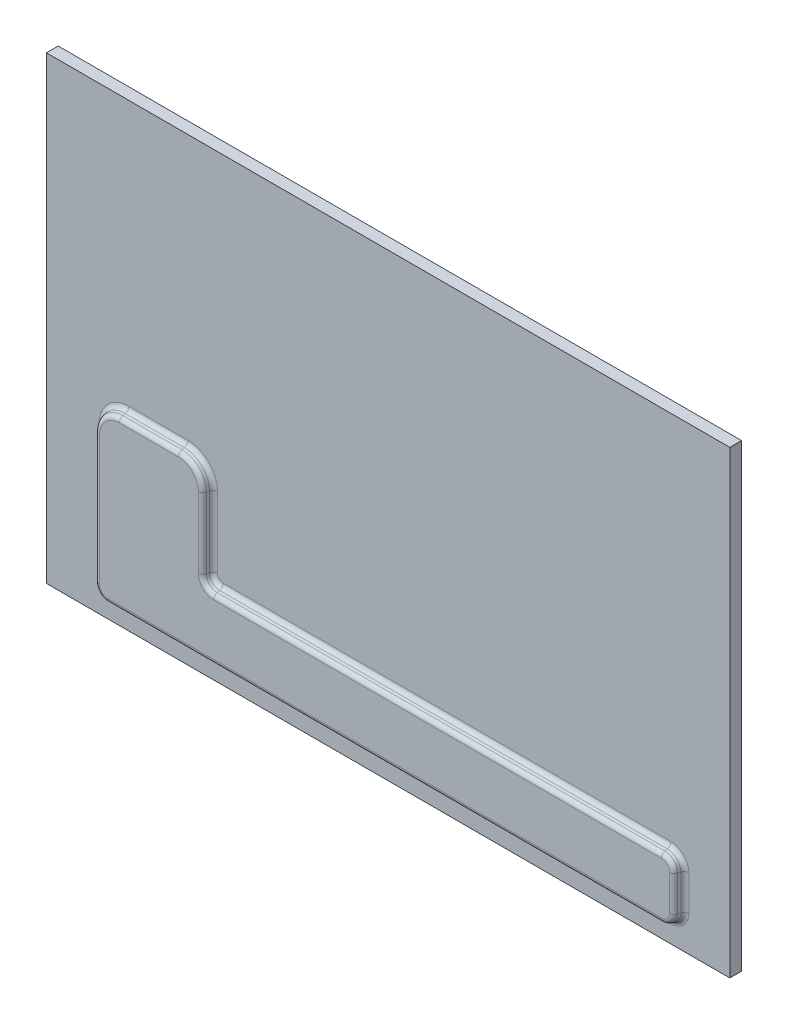
SolidWorks part; units mm, degrees
ref_plane "前视基准面" through (0, 0, 0) normal (0, 0, 1) x (1, 0, 0)
ref_plane "上视基准面" through (0, 0, 0) normal (0, 1, 0) x (1, 0, 0)
ref_plane "右视基准面" through (0, 0, 0) normal (1, 0, 0) x (0, 0, -1)
sketch "草图1" plane through (0, 0, 0) normal (0, 0, 1) x (1, 0, 0)
  line L1 (145, -97.5) -> (-145, -97.5)
  line L2 (145, -97.5) -> (145, 97.5)
  line L3 (145, 97.5) -> (-145, 97.5)
  line L4 (-145, -97.5) -> (-145, 97.5)
  line L5 (145, -97.5) -> (-145, 97.5) construction
  line L6 (145, 97.5) -> (-145, -97.5) construction
  point P0 (0, 0)
  dimension "D1" = 290
  dimension "D2" = 195
extrude "凸台-拉伸1" add sketch "草图1" along normal blind 5
sketch "草图2" plane through (0, 0, 5) normal (0, 0, 1) x (1, 0, 0)
  line L0 (-75, -17.5) -> (-120, -17.5)
  line L1 (-120, -17.5) -> (-120, -87.5)
  line L2 (-120, -87.5) -> (125, -87.5)
  line L3 (125, -87.5) -> (125, -62.5)
  line L4 (125, -62.5) -> (-75, -62.5)
  line L5 (-75, -62.5) -> (-75, -17.5)
  line L7 (-145, 97.5) -> (-145, -97.5) construction
  line L8 (145, 97.5) -> (-145, 97.5) construction
  dimension "D1" = 45
  dimension "D2" = 70
  dimension "D3" = 25
  dimension "D4" = 25
  dimension "D5" = 245
  dimension "D6" = 115
extrude "凸台-拉伸2" add sketch "草图2" along normal blind 4
fillet "圆角1" radius 5 4 edges at (125, -87.5, 7) (-120, -87.5, 7) (125, -62.5, 7) (-75, -62.5, 7)
fillet "圆角2" radius 10 2 edges at (-75, -17.5, 7) (-120, -17.5, 7)
draft "拔模2" type of draft neutral plane draft angle 15 faces to draft 12 face at (-73.0178, -60.5178, 7) face at (123.0178, -64.4822, 7) face at (123.0178, -85.5178, 7) face at (125, -75, 7) face at (25, -62.5, 7) face at (-75, -42.5, 7) face at (-78.9645, -21.4645, 7) face at (-97.5, -17.5, 7) face at (-116.0355, -21.4645, 7) face at (-120, -55, 7) face at (-118.0178, -85.5178, 7) face at (2.5, -87.5, 7) neutral plane through (0, 0, 9) neutral plane normal (0, 0, 1) parameters "D1"=15
fillet "圆角3" radius 2 24 edges at (-73.9282, -42.5, 5) (-77.1711, -19.6711, 5) (-97.5, -16.4282, 5) (-117.8289, -19.6711, 5) (-121.0718, -55, 5) (-119.2934, -86.7934, 5) (126.0718, -75, 5) (124.2934, -86.7934, 5) (-75, -42.5, 9) (-77.9289, -20.4289, 9) (-97.5, -17.5, 9) (-117.0711, -20.4289, 9) (-120, -55, 9) (-118.5355, -86.0355, 9) (125, -75, 9) (123.5355, -86.0355, 9) (25, -61.4282, 5) (25, -62.5, 9) (2.5, -88.5718, 5) (2.5, -87.5, 9) (-72.7777, -60.2777, 5) (124.2934, -63.2066, 5) (-73.5355, -61.0355, 9) (123.5355, -63.9645, 9)
sketch "方向草图" plane through (0, 0, 5) normal (0, 0, 1) x (1, 0, 0)
  line L0 (-122.6065, -82.5) -> (-122.6065, -27.5) construction
  line L1 (-110, -14.8935) -> (-85, -14.8935) construction
  line L2 (-72.3935, -27.5) -> (-72.3935, -57.5) construction
  line L3 (-70, -59.8935) -> (120, -59.8935) construction
  line L4 (127.6065, -67.5) -> (127.6065, -82.5) construction
  line L5 (120, -90.1065) -> (-115, -90.1065) construction
  line L6 (-145, 97.5) -> (-145, -97.5) construction
  line L7 (-145, -97.5) -> (145, -97.5) construction
  line L8 (145, -97.5) -> (145, 97.5) construction
  line L9 (145, 97.5) -> (-145, 97.5) construction
  line L10 (-122.6065, -82.5) -> (-122.6065, -27.5)
  line L11 (-110, -14.8935) -> (-85, -14.8935)
  line L12 (-72.3935, -27.5) -> (-72.3935, -57.5)
  line L13 (-70, -59.8935) -> (120, -59.8935)
  line L14 (127.6065, -67.5) -> (127.6065, -82.5)
  line L15 (120, -90.1065) -> (-115, -90.1065)
  line L16 (-145, 97.5) -> (-145, -97.5) construction
  line L17 (-145, -97.5) -> (145, -97.5) construction
  line L18 (145, -97.5) -> (145, 97.5) construction
  line L19 (145, 97.5) -> (-145, 97.5) construction
  arc A0 (-122.6065, -82.5) -> (-115, -90.1065) centre (-115, -82.5) ccw construction
  arc A1 (-110, -14.8935) -> (-122.6065, -27.5) centre (-110, -27.5) ccw construction
  arc A2 (-72.3935, -27.5) -> (-85, -14.8935) centre (-85, -27.5) ccw construction
  arc A3 (-72.3935, -57.5) -> (-70, -59.8935) centre (-70, -57.5) ccw construction
  arc A4 (127.6065, -67.5) -> (120, -59.8935) centre (120, -67.5) ccw construction
  arc A5 (120, -90.1065) -> (127.6065, -82.5) centre (120, -82.5) ccw construction
  arc A6 (-122.6065, -82.5) -> (-115, -90.1065) centre (-115, -82.5) ccw
  arc A7 (-110, -14.8935) -> (-122.6065, -27.5) centre (-110, -27.5) ccw
  arc A8 (-72.3935, -27.5) -> (-85, -14.8935) centre (-85, -27.5) ccw
  arc A9 (-72.3935, -57.5) -> (-70, -59.8935) centre (-70, -57.5) ccw
  arc A10 (127.6065, -67.5) -> (120, -59.8935) centre (120, -67.5) ccw
  arc A11 (120, -90.1065) -> (127.6065, -82.5) centre (120, -82.5) ccw
  point P20 (0, 0)
other "成形工具1"
